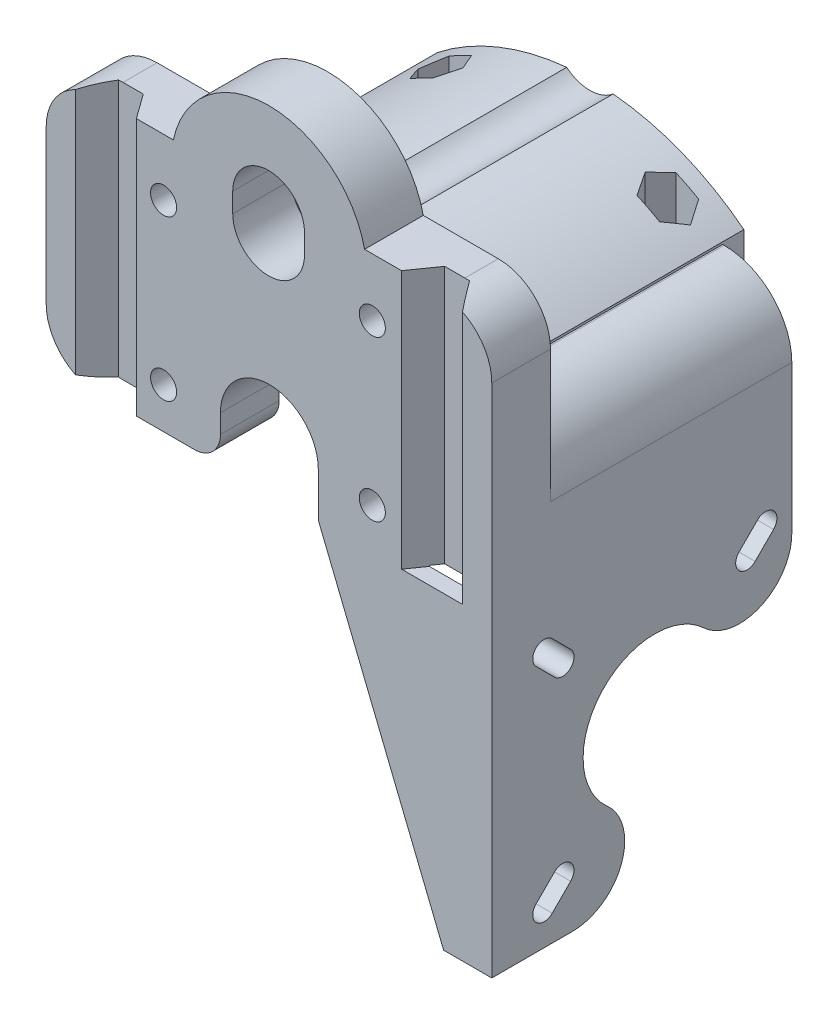
SolidWorks part; units mm, degrees
ref_plane "Front Plane" through (0, 0, 0) normal (0, 0, 1) x (1, 0, 0)
ref_plane "Top Plane" through (0, 0, 0) normal (0, 1, 0) x (1, 0, 0)
ref_plane "Right Plane" through (0, 0, 0) normal (1, 0, 0) x (0, 0, -1)
sketch "Sketch1" plane through (0, 0, 0) normal (0, 0, 1) x (1, 0, 0)
  line L0 (0, 0) -> (-7.3836, 0)
  line L1 (-7.3836, 0) -> (-26.6, 47.5)
  line L2 (-26.6, 47.5) -> (-26.6, 54.25)
  line L3 (0, 0) -> (0, 79)
  line L4 (-8, 87) -> (-19.5, 87)
  line L5 (-48.8167, 86.8649) -> (-60.3167, 86.8649)
  line L6 (-68.3167, 78.8649) -> (-68.3167, 55.3649)
  line L7 (-60.3167, 47.3649) -> (-45.6, 47.3649)
  line L8 (-41.6, 54.25) -> (-41.6, 51.3649)
  line L9 (-48.8167, 86.8649) -> (-19.5, 87) construction
  line L13 (-50.3167, 78.1149) -> (-50.3167, 53.6149) construction
  line L14 (-50.3167, 53.6149) -> (-18.3167, 53.6149) construction
  line L15 (-18.3167, 53.6149) -> (-18.3167, 78.1149) construction
  line L16 (-18.3167, 78.1149) -> (-50.3167, 78.1149) construction
  arc A0 (-19.5, 87) -> (-48.8167, 86.8649) centre (-34.1437, 83.75) ccw
  arc A1 (-26.6, 54.25) -> (-41.6, 54.25) centre (-34.1, 54.25) ccw
  arc A2 (0, 79) -> (-8, 87) centre (-8, 79) ccw
  arc A3 (-60.3167, 86.8649) -> (-68.3167, 78.8649) centre (-60.3167, 78.8649) ccw
  arc A4 (-68.3167, 55.3649) -> (-60.3167, 47.3649) centre (-60.3167, 55.3649) ccw
  arc A5 (-45.6, 47.3649) -> (-41.6, 51.3649) centre (-45.6, 51.3649) ccw
  circle A8 centre (-50.3167, 78.1149) radius 2
  circle A9 centre (-18.3167, 78.1149) radius 2
  circle A10 centre (-50.3167, 53.6149) radius 2
  circle A11 centre (-18.3167, 53.6149) radius 2
  point P16 (0, 87)
  point P19 (-68.3167, 86.8649)
  point P22 (-68.3167, 47.3649)
  dimension "D1" = 7.3836
  dimension "D5" = 15
  dimension "D11" = 7.5
  dimension "D13" = 8
  dimension "D14" = 8
  dimension "D15" = 8
  dimension "D16" = 4
  dimension "D20" = 4
  dimension "D23" = 4
  dimension "D24" = 4
  dimension "D25" = 4
  dimension "D2" = 87
  dimension "D3" = 19.5
  dimension "D4" = 19.5
  dimension "D6" = 3.25
  dimension "D7" = 29.317
  dimension "D8" = 39.5
  dimension "D9" = 47.5
  dimension "D10" = 26.6
  dimension "D12" = 6.75
  dimension "D21" = 8.75
  dimension "D22" = 18
  dimension "D26" = 32
  dimension "D27" = 24.5
extrude "Boss-Extrude1" add sketch "Sketch1" along normal blind 9
sketch "Sketch3" plane through (0, 0, 0) normal (0, 0, -1) x (-1, 0, 0)
  line L0 (0, 0) -> (5.4, 0)
  line L1 (7.3836, 0) -> (0, 0) construction
  line L2 (5.4, 0) -> (5.4, 58.675)
  line L3 (10.475, 63.75) -> (57.6, 63.75)
  line L4 (57.6, 63.75) -> (57.6, 69.45)
  line L5 (10.6, 69.1) -> (10.375, 69.1)
  line L6 (0, 0) -> (0, 79) construction
  line L7 (0, 58.725) -> (0, 0)
  line L8 (10.6, 69.1) -> (10.6, 69.45)
  line L9 (10.6, 69.45) -> (57.6, 69.45) construction
  arc A0 (10.6, 69.45) -> (57.6, 69.45) centre (34.1, 39.5878) cw
  arc A1 (5.4, 58.675) -> (10.475, 63.75) centre (10.475, 58.675) cw
  arc A2 (10.375, 69.1) -> (0, 58.725) centre (10.375, 58.725) ccw
  point P18 (0, 69.1)
  dimension "D1" = 5.4
  dimension "D5" = 10.6
  dimension "D7" = 5.075
  dimension "D8" = 10.375
  dimension "D9" = 0.35
  dimension "D10" = 38
  dimension "D2" = 63.75
  dimension "D3" = 69.1
  dimension "D4" = 57.6
  dimension "D6" = 69.45
extrude "Boss-Extrude2" add sketch "Sketch3" along normal blind 40.25 contours A0 L4 L3 A1 L2 L0 L7 A2 L5 L8
sketch "Sketch5" plane through (0, 0, 9) normal (0, 0, 1) x (1, 0, 0)
  line L0 (-34.2167, 84.6149) -> (-34.2167, 81.6149) construction
  line L1 (-28.7167, 84.6149) -> (-28.7167, 81.6149)
  line L2 (-39.7167, 84.6149) -> (-39.7167, 81.6149)
  line L3 (-48.8167, 86.8649) -> (-60.3167, 86.8649) construction
  line L4 (-68.3167, 78.8649) -> (-68.3167, 55.3649) construction
  arc A0 (-28.7167, 84.6149) -> (-39.7167, 84.6149) centre (-34.2167, 84.6149) ccw
  arc A1 (-39.7167, 81.6149) -> (-28.7167, 81.6149) centre (-34.2167, 81.6149) ccw
  point P2 (-34.2167, 83.1149)
  dimension "D2" = 5.5
  dimension "D1" = 3
  dimension "D3" = 2.25
  dimension "D4" = 28.6
extrude "Cut-Extrude1" cut sketch "Sketch5" against normal blind 50
sketch "Sketch6" plane through (0, 0, 0) normal (1, 0, 0) x (0, 0, -1)
  line L0 (-9, 0) -> (-9, 79) construction
  line L1 (-9, 0) -> (40.25, 0) construction
  line L2 (37, 36.0564) -> (37, 82.8388)
  line L3 (37, 82.8388) -> (40.25, 82.8388)
  line L4 (40.25, 82.8388) -> (40.25, 0)
  line L5 (40.25, 0) -> (37.9285, 0)
  line L6 (-9, 0) -> (37.9285, 0)
  line L7 (1.8589, 36.366) -> (-0.97, 39.194) construction
  line L8 (0.6216, 35.1284) -> (-2.2073, 37.9564)
  line L9 (3.0961, 37.6036) -> (0.2673, 40.4316)
  line L10 (16, 22.2) -> (16, 52.04) construction
  line L11 (16, 22.2) -> (-24.0425, 22.2) construction
  line L12 (1.8589, 8.034) -> (-0.97, 5.206) construction
  line L13 (0.6216, 9.2716) -> (-2.2072, 6.4436)
  line L14 (3.0961, 6.7964) -> (0.2673, 3.9684)
  line L15 (30.1411, 36.366) -> (32.97, 39.194) construction
  line L16 (31.3784, 35.1284) -> (34.2073, 37.9564)
  line L17 (28.9039, 37.6036) -> (31.7328, 40.4316)
  arc A0 (23.5263, 30.2221) -> (8.6915, 13.9789) centre (16, 22.2) ccw
  arc A1 (3.3762, 0) -> (8.6915, 13.9789) centre (3.3762, 8) ccw
  arc A2 (23.5263, 30.2221) -> (37, 36.0564) centre (29, 36.0564) ccw
  arc A3 (0.6216, 35.1284) -> (3.0961, 37.6036) centre (1.8589, 36.366) ccw
  arc A4 (0.2673, 40.4316) -> (-2.2073, 37.9564) centre (-0.97, 39.194) ccw
  arc A5 (0.6216, 9.2716) -> (3.0961, 6.7964) centre (1.8589, 8.034) cw
  arc A6 (0.2673, 3.9684) -> (-2.2072, 6.4436) centre (-0.97, 5.206) cw
  arc A7 (31.3784, 35.1284) -> (28.9039, 37.6036) centre (30.1411, 36.366) cw
  arc A8 (31.7328, 40.4316) -> (34.2073, 37.9564) centre (32.97, 39.194) cw
  point P20 (0.4444, 37.78)
  point P29 (0.4444, 6.62)
  point P36 (31.5556, 37.78)
  line M8 (-9, 0) -> (40.25, 0)
  line M9 (40.25, 0) -> (40.25, 58.725)
  line M10 (40.25, 58.725) -> (0, 58.725)
  dimension "D1" = 22
  dimension "D6" = 16
  dimension "D7" = 16
  dimension "D10" = 1.75
  dimension "D2" = 25
  dimension "D3" = 22.2
  dimension "D4" = 46
  dimension "D5" = 82.8388
  dimension "D8" = 2.3215
  dimension "D9" = 4
  dimension "D11" = 2.828
  dimension "D12" = 8.03
  dimension "D13" = 36.366
extrude "Cut-Extrude2" cut sketch "Sketch6" against normal blind 10.6 contours A2 A0 A1 L6 L2 M8 M9 M10 | L9 A4 L8 A3 | A8 L17 A7 L16 | A6 L14 A5 L13 | L4 L3 L2 M10
sketch "Sketch7" plane through (0, 86.8649, 0) normal (0, 1, 0) x (1, 0, 0)
  line L0 (-13.833, -9) -> (-11.1, -5.12)
  line L1 (-8, -9) -> (-19.5, -9) construction
  line L2 (-11.1, -5.12) -> (-7.3, -5.12)
  line L3 (-7.3, -5.12) -> (-4.5, -9)
  line L4 (-63.8167, -9) -> (-61.0167, -5.217)
  line L5 (-48.8167, -9) -> (-60.3167, -9) construction
  line L6 (-61.0167, -5.217) -> (-57.2167, -5.217)
  line L7 (-57.2167, -5.217) -> (-54.4867, -9)
  line L8 (-54.4867, -9) -> (-63.8167, -9)
  line L9 (-13.833, -9) -> (-4.5, -9)
  line L10 (-19.5, -9) -> (-19.5, 0) construction
  line L11 (-48.8167, -9) -> (-48.8167, 0) construction
  line L12 (-57.6, 40.25) -> (-57.6, 0) construction
  line L13 (-37.763, 0) -> (-57.6, 0) construction
  line L14 (-34.2051, 40.25) -> (-34.1584, -9) construction
  line L15 (-30.6471, 40.25) -> (-37.763, 40.25) construction
  line L16 (-48.8167, -9) -> (-19.5, -9) construction
  line L17 (-37.763, 40.25) -> (-57.6, 40.25) construction
  line L18 (-51.6, 34.75) -> (-51.6, 6) construction
  circle A0 centre (-51.6, 34.75) radius 1.8
  circle A1 centre (-51.6, 6) radius 1.8
  circle A2 centre (-16.7452, 6.0331) radius 1.8
  circle A3 centre (-16.7997, 34.783) radius 1.8
  dimension "D1" = 15
  dimension "D10" = 3.6
  dimension "D11" = 6
  dimension "D13" = 3.6
  dimension "D14" = 5.5
  dimension "D2" = 5.667
  dimension "D3" = 3.88
  dimension "D4" = 3.8
  dimension "D5" = 8.4
  dimension "D6" = 3.8
  dimension "D7" = 15
  dimension "D8" = 5.67
  dimension "D9" = 8.4
  dimension "D12" = 6
extrude "Cut-Extrude3" cut sketch "Sketch7" against normal blind 39.5 and the other way blind 39.5
sketch "Sketch8" plane through (0, 86.8649, 0) normal (0, 1, 0) x (1, 0, 0)
  line L0 (-34.2051, 40.25) -> (-34.1584, 0) construction
  line L1 (-48.1359, 34.75) -> (-49.8679, 37.75)
  line L2 (-49.8679, 37.75) -> (-53.3321, 37.75)
  line L3 (-53.3321, 37.75) -> (-55.0641, 34.75)
  line L4 (-55.0641, 34.75) -> (-53.3321, 31.75)
  line L5 (-53.3321, 31.75) -> (-49.8679, 31.75)
  line L6 (-49.8679, 31.75) -> (-48.1359, 34.75)
  line L7 (-30.6471, 40.25) -> (-37.763, 40.25) construction
  line L8 (-19.5, 0) -> (-48.8167, 0) construction
  line L10 (-48.1359, 6) -> (-49.8679, 9)
  line L11 (-49.8679, 9) -> (-53.3321, 9)
  line L12 (-53.3321, 9) -> (-55.0641, 6)
  line L13 (-55.0641, 6) -> (-53.3321, 3)
  line L14 (-53.3321, 3) -> (-49.8679, 3)
  line L15 (-49.8679, 3) -> (-48.1359, 6)
  line L17 (-18.4697, 9.0364) -> (-15.0056, 9.0445)
  line L18 (-20.1948, 6.0324) -> (-18.4697, 9.0364)
  line L19 (-18.4558, 3.0365) -> (-20.1948, 6.0324)
  line L20 (-14.9917, 3.0445) -> (-18.4558, 3.0365)
  line L21 (-13.2666, 6.0485) -> (-14.9917, 3.0445)
  line L22 (-15.0056, 9.0445) -> (-13.2666, 6.0485)
  line L23 (-18.5225, 31.7864) -> (-20.2615, 34.7823)
  line L24 (-20.2615, 34.7823) -> (-18.5364, 37.7864)
  line L25 (-18.5364, 37.7864) -> (-15.0723, 37.7944)
  line L26 (-15.0723, 37.7944) -> (-13.3333, 34.7984)
  line L27 (-13.3333, 34.7984) -> (-15.0584, 31.7944)
  line L28 (-15.0584, 31.7944) -> (-18.5225, 31.7864)
  circle A0 centre (-51.6, 34.75) radius 3 construction
  circle A1 centre (-51.6, 6) radius 3 construction
  dimension "D1" = 6
extrude "Cut-Extrude4" cut sketch "Sketch8" against normal blind 20.85
sketch "Sketch9" plane through (0, 0, 0) normal (0, 0, -1) x (-1, 0, 0)
  circle A0 centre (18.3167, 78.1149) radius 4.05
  circle A1 centre (50.3167, 78.1149) radius 4.05
  circle A2 centre (18.3167, 53.6149) radius 4.05
  circle A3 centre (50.3167, 53.6149) radius 4.05
  dimension "D1" = 8.1
  dimension "D2" = 8.1
  dimension "D3" = 8.1
  dimension "D4" = 8.1
extrude "Cut-Extrude5" cut sketch "Sketch9" against normal blind 2.4
sketch "Sketch10" plane through (0, 0, 0) normal (0, 0, -1) x (-1, 0, 0)
  line L0 (26.6, 47.5) -> (5.4, 47.5)
  line L1 (5.4, 40.6506) -> (5.4, 58.675) construction
  line L2 (5.4, 47.5) -> (5.4, 0)
  line L3 (5.4, 0) -> (7.3836, 0)
  line L4 (7.3836, 0) -> (26.6, 47.5)
extrude "Cut-Extrude6" cut sketch "Sketch10" against normal blind 6.5
